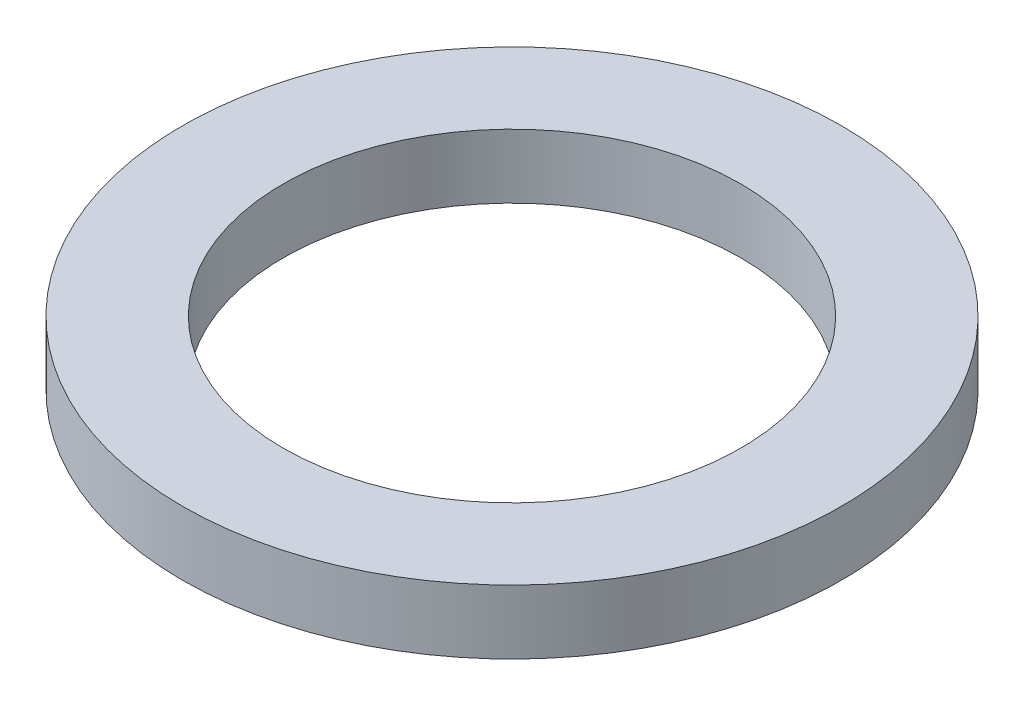
SolidWorks part; units mm, degrees
ref_plane "Plan1" through (0, 0, 0) normal (0, 0, 1) x (1, 0, 0)
ref_plane "Plan2" through (0, 0, 0) normal (0, 1, 0) x (1, 0, 0)
ref_plane "Plan3" through (0, 0, 0) normal (1, 0, 0) x (0, 0, -1)
sketch "Esquisse1" plane through (0, 0, 0) normal (0, 0, 1) x (1, 0, 0)
  line L0 (0, 60) -> (0, -60) construction
  line L1 (12.5, 0) -> (18, 0)
  line L2 (12.5, 0) -> (12.5, 3.5)
  line L3 (12.5, 3.5) -> (18, 3.5)
  line L4 (18, 0) -> (18, 3.5)
  dimension "D1" = 18
  dimension "D2" = 12.5
  dimension "D3" = 3.5
revolve "Base-Révolution" add sketch "Esquisse1" angle 360 about L0
